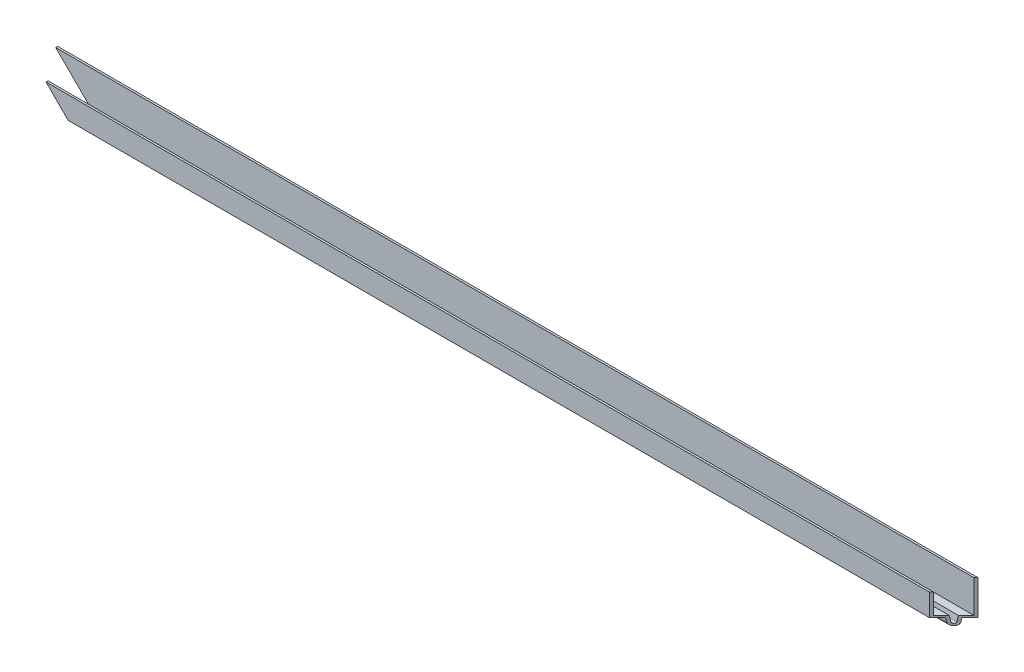
SolidWorks part; units mm, degrees
material "6063-O"
ref_plane "Front Plane" through (0, 0, 0) normal (0, 0, 1) x (1, 0, 0)
ref_plane "Top Plane" through (0, 0, 0) normal (0, 1, 0) x (1, 0, 0)
ref_plane "Right Plane" through (0, 0, 0) normal (1, 0, 0) x (0, 0, -1)
other "Configuration Table"
sketch "Sketch1" plane through (0, 0, 0) normal (1, 0, 0) x (0, 0, -1)
  line L0 (7.62, 0) -> (7.62, -21.844)
  line L1 (7.62, -21.844) -> (2.54, -21.844)
  line L2 (-2.54, -21.844) -> (-2.2022, -24.2477)
  line L3 (2.2022, -24.2477) -> (2.54, -21.844)
  line L4 (-2.54, -21.844) -> (-7.62, -21.844)
  line L5 (-7.62, -21.844) -> (-7.62, -7.874)
  line L6 (6.35, 0) -> (6.35, -20.574)
  line L7 (6.35, -20.574) -> (1.436, -20.574)
  line L8 (0.9445, -24.0709) -> (1.436, -20.574)
  line L9 (-1.436, -20.574) -> (-0.9445, -24.0709)
  line L10 (-1.436, -20.574) -> (-6.35, -20.574)
  line L11 (-6.35, -20.574) -> (-6.35, -7.874)
  line L12 (7.62, 0) -> (6.35, 0)
  line L13 (-7.62, -7.874) -> (-6.35, -7.874)
  line L14 (0, 0) -> (0, -30.4009) construction
  arc A0 (-2.2022, -24.2477) -> (2.2022, -24.2477) centre (0, -23.9382) ccw
  arc A1 (-0.9445, -24.0709) -> (0.9445, -24.0709) centre (0, -23.9382) ccw
  dimension "D1" = 15.24
  dimension "D2" = 4.318
  dimension "D3" = 21.844
  dimension "D4" = 13.97
  dimension "D5" = 12.7
  dimension "D6" = 82
  dimension "D7" = 5.08
extrude "Boss-Extrude1" add sketch "Sketch1" along normal mid plane 579.4375
sketch "Sketch4" plane through (0, 0, 0) normal (0, 1, 0) x (1, 0, 0)
  line L0 (-289.7187, 7.62) -> (-274.4787, -7.62)
  line L1 (289.7187, -7.62) -> (-289.7187, -7.62) construction
  line L2 (-274.4787, -7.62) -> (-289.7187, -7.62)
  line L3 (-289.7187, -7.62) -> (-289.7187, 7.62)
extrude "Cut-Top-Left-Front" [suppressed] cut sketch "Sketch4" against normal through all
sketch "Sketch9" plane through (0, 0, 7.62) normal (0, 0, 1) x (1, 0, 0)
  line L0 (-289.7187, -26.162) -> (-263.5567, 0)
  line L1 (289.7187, 0) -> (-289.7187, 0) construction
  line L2 (-263.5567, 0) -> (-289.7187, 0)
  line L3 (-289.7187, 0) -> (-289.7187, -26.162)
extrude "Cut-Front-Left-Top" [suppressed] cut sketch "Sketch9" against normal through all
sketch "Sketch11" plane through (0, 0, 7.62) normal (0, 0, 1) x (1, 0, 0)
  line L0 (289.7187, 0) -> (263.5567, -26.162)
  line L1 (-289.7187, -26.162) -> (289.7187, -26.162) construction
  line L2 (263.5567, -26.162) -> (289.7187, -26.162)
  line L3 (289.7187, -26.162) -> (289.7187, 0)
extrude "Cut-Front-Right-Bottom" [suppressed] cut sketch "Sketch11" against normal through all
sketch "Sketch2" plane through (0, 0, 0) normal (0, 1, 0) x (1, 0, 0)
  line L0 (289.7187, 7.62) -> (274.4787, -7.62)
  line L1 (289.7187, -7.62) -> (-289.7187, -7.62) construction
  line L2 (274.4787, -7.62) -> (289.7187, -7.62)
  line L3 (289.7187, -7.62) -> (289.7187, 7.62)
extrude "Cut-Top-Right-Front" cut sketch "Sketch2" against normal through all
sketch "Sketch7" plane through (0, 0, 7.62) normal (0, 0, 1) x (1, 0, 0)
  line L0 (152.4, -26.162) -> (126.238, 0)
  line L2 (126.238, 0) -> (152.4, 0)
  line L4 (152.4, 0) -> (152.4, -26.162)
  line L5 (152.4, -7.874) -> (152.4, -21.844) construction
  line L6 (288.4487, 0) -> (-289.7187, 0) construction
extrude "Cut-Front-Right-Top" [suppressed] cut sketch "Sketch7" against normal through all
sketch "Sketch12" plane through (0, 0, 7.62) normal (0, 0, 1) x (1, 0, 0)
  line L0 (-289.7187, 0) -> (-263.5567, -26.162)
  line L1 (-289.7187, -26.162) -> (282.0987, -26.162) construction
  line L2 (-263.5567, -26.162) -> (-289.7187, -26.162)
  line L3 (-289.7187, -26.162) -> (-289.7187, 0)
extrude "Cut-Front-Left-Bottom" cut sketch "Sketch12" against normal through all
